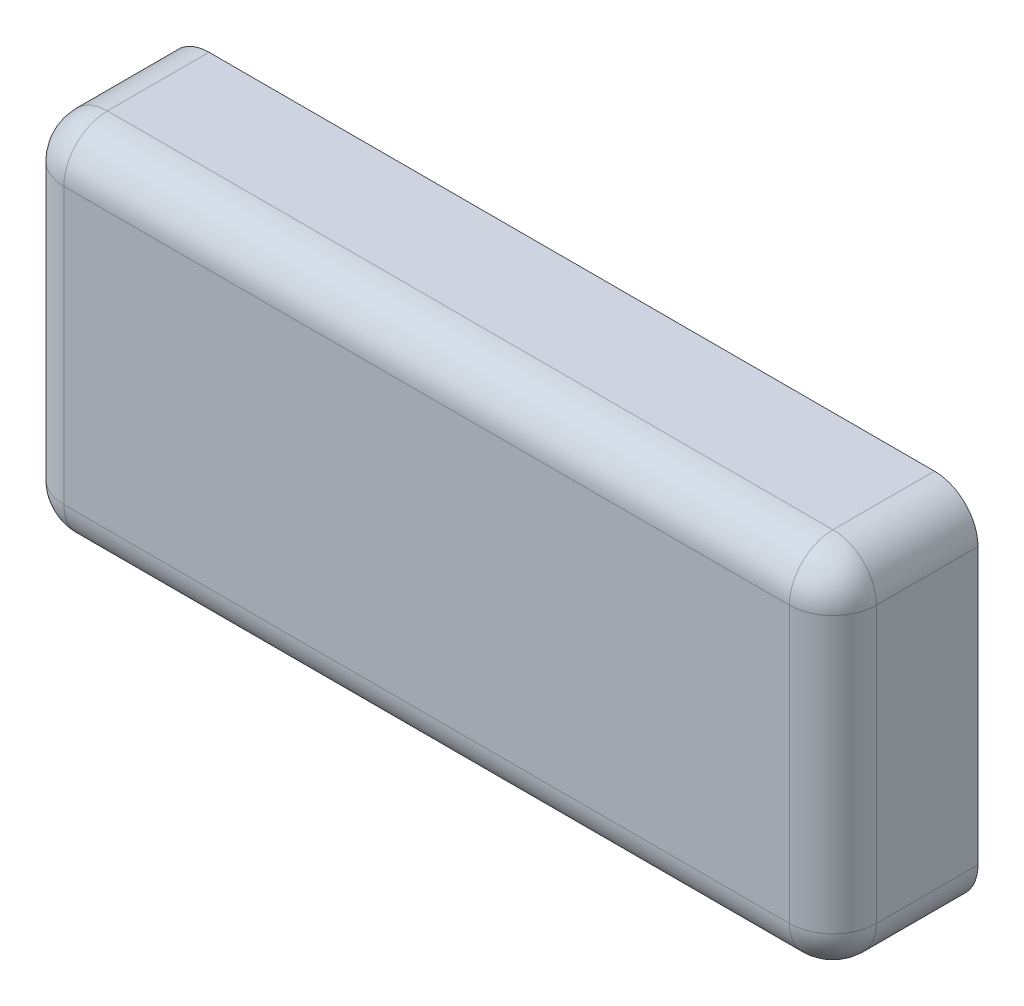
SolidWorks part; units mm, degrees
ref_plane "Front Plane" through (0, 0, 0) normal (0, 0, 1) x (1, 0, 0)
ref_plane "Top Plane" through (0, 0, 0) normal (0, 1, 0) x (1, 0, 0)
ref_plane "Right Plane" through (0, 0, 0) normal (1, 0, 0) x (0, 0, -1)
sketch "Sketch1" plane through (0, 0, 0) normal (0, 0, 1) x (1, 0, 0)
  line L1 (-7.112, -3.175) -> (7.112, -3.175)
  line L2 (-7.112, -3.175) -> (-7.112, 3.175)
  line L3 (-7.112, 3.175) -> (7.112, 3.175)
  line L4 (7.112, -3.175) -> (7.112, 3.175)
  line L5 (-7.112, -3.175) -> (7.112, 3.175) construction
  line L6 (-7.112, 3.175) -> (7.112, -3.175) construction
  point P0 (0, 0)
  dimension "D1" = 6.35
  dimension "D2" = 14.224
extrude "Extrude1" add sketch "Sketch1" along normal blind 2.54
fillet "Fillet1" radius 0.762 4 edges at (-7.112, -3.175, 1.27) (-7.112, 3.175, 1.27) (7.112, 3.175, 1.27) (7.112, -3.175, 1.27)
fillet "Fillet2" radius 0.762 8 edges at (-6.8888, 2.9518, 2.54) (0, 3.175, 2.54) (6.8888, 2.9518, 2.54) (7.112, 0, 2.54) (6.8888, -2.9518, 2.54) (0, -3.175, 2.54) (-6.8888, -2.9518, 2.54) (-7.112, 0, 2.54)
